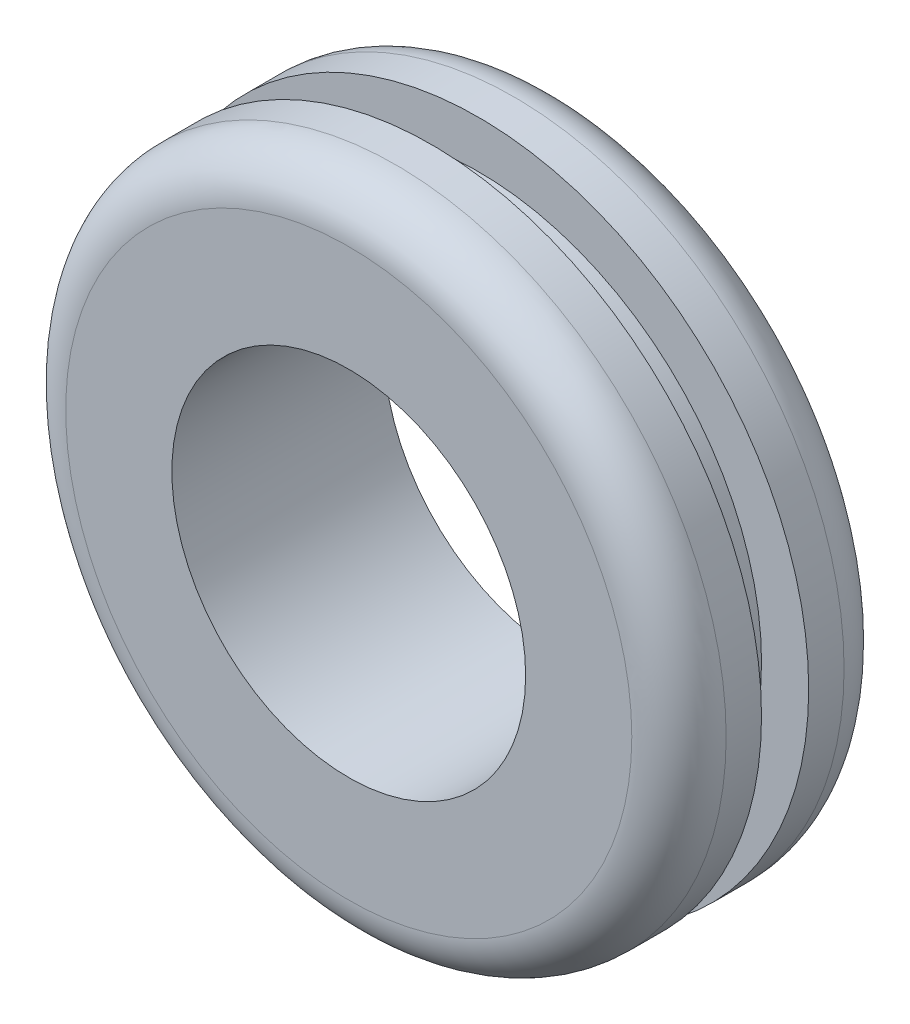
SolidWorks part; units mm, degrees
material "Caoutchouc silicone"
ref_plane "Plan de face" through (0, 0, 0) normal (0, 0, 1) x (1, 0, 0)
ref_plane "Plan de dessus" through (0, 0, 0) normal (0, 1, 0) x (1, 0, 0)
ref_plane "Plan de droite" through (0, 0, 0) normal (1, 0, 0) x (0, 0, -1)
sketch "Esquisse1" plane through (0, 0, 0) normal (0, 0, 1) x (1, 0, 0)
  circle A0 centre (0, 0) radius 14
  dimension "D1" = 28
extrude "Boss.-Extru.1" add sketch "Esquisse1" along normal mid plane 9
fillet "Congé1" radius 2 2 edges at (14, 0, -4.5) (14, 0, 4.5)
sketch "Esquisse14" plane through (0, 0, 0) normal (1, 0, 0) x (0, 0, -1)
  line L0 (0, 14) -> (0, 8.8076) construction
  line L1 (2.5, 14) -> (-2.5, 14) construction
  line L2 (-11.5179, 0) -> (15.7494, 0) construction
  line L3 (-1, 14) -> (1, 14)
  line L4 (-1, 14) -> (-1, 12)
  line L5 (-1, 12) -> (1, 12)
  line L6 (1, 14) -> (1, 12)
  dimension "D1" = 1
  dimension "D2" = 1
  dimension "D3" = 2
  dimension "D4" = 14
revolve "Enlèvement de matière-Révolution2" cut sketch "Esquisse14" angle 360 about L2
sketch "Esquisse15" plane through (0, 0, 4.5) normal (0, 0, 1) x (1, 0, 0)
  circle A0 centre (0, 0) radius 7.5
  dimension "D1" = 15
extrude "Enlèv. mat.-Extru.2" cut sketch "Esquisse15" against normal through all
